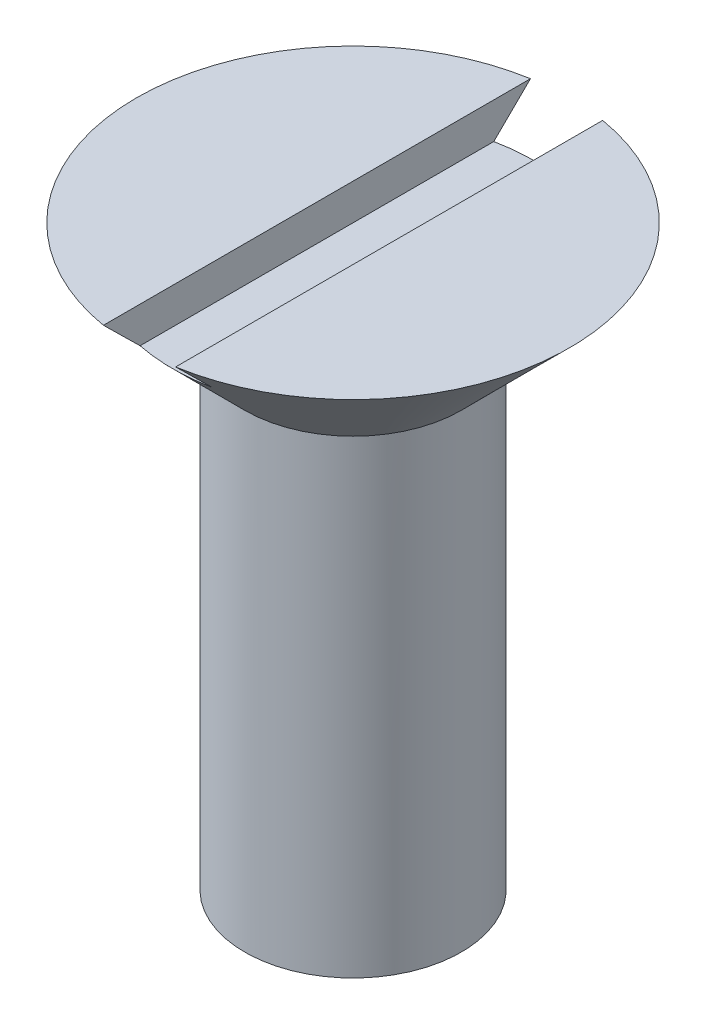
SolidWorks part; units mm, degrees
ref_plane "Front Plane" through (0, 0, 0) normal (0, 0, 1) x (1, 0, 0)
ref_plane "Top Plane" through (0, 0, 0) normal (0, 1, 0) x (1, 0, 0)
ref_plane "Right Plane" through (0, 0, 0) normal (1, 0, 0) x (0, 0, -1)
sketch "Sketch2" plane through (0, 0, 0) normal (0, 1, 0) x (1, 0, 0)
  circle A0 centre (0, 0) radius 3
extrude "Boss-Extrude1" add sketch "Sketch2" along normal mid plane 13
sketch "Sketch5" plane through (0, 0, 0) normal (0, 0, 1) x (1, 0, 0)
  line L0 (-3, -6.5) -> (0, -8.2321)
  line L1 (0, -6.5) -> (0, -8.2321)
  line L3 (-3, -6.5) -> (3, -6.5) construction
  line L4 (-3, -6.5) -> (0, -6.5)
  dimension "D1" = 60
revolve "Revolve2" add sketch "Sketch5" angle 360 about L1
sketch "Sketch6" plane through (0, 0, 0) normal (0, 0, 1) x (1, 0, 0)
  line L0 (0, 6.5) -> (0, 9.5)
  line L1 (3, 6.5) -> (-3, 6.5) construction
  line L2 (0, 9.5) -> (6, 9.5)
  line L3 (3, 6.5) -> (6, 9.5)
  line L4 (0, 9.5) -> (0, 8.5)
  line L5 (3, 6.5) -> (0, 6.5)
  dimension "D1" = 45
revolve "Revolve3" add sketch "Sketch6" angle 360 about L0
sketch "Sketch7" plane through (0, 0, 0) normal (0, 0, 1) x (1, 0, 0)
  line L0 (1, 9.5) -> (-1, 9.5)
  line L1 (6, 9.5) -> (-6, 9.5) construction
  line L2 (-1, 9.5) -> (-1, 8.5)
  line L3 (-1, 8.5) -> (1, 8.5)
  line L4 (1, 8.5) -> (1, 9.5)
  point P5 (0, 9.5)
extrude "Cut-Extrude1" cut sketch "Sketch7" against normal mid plane 14
